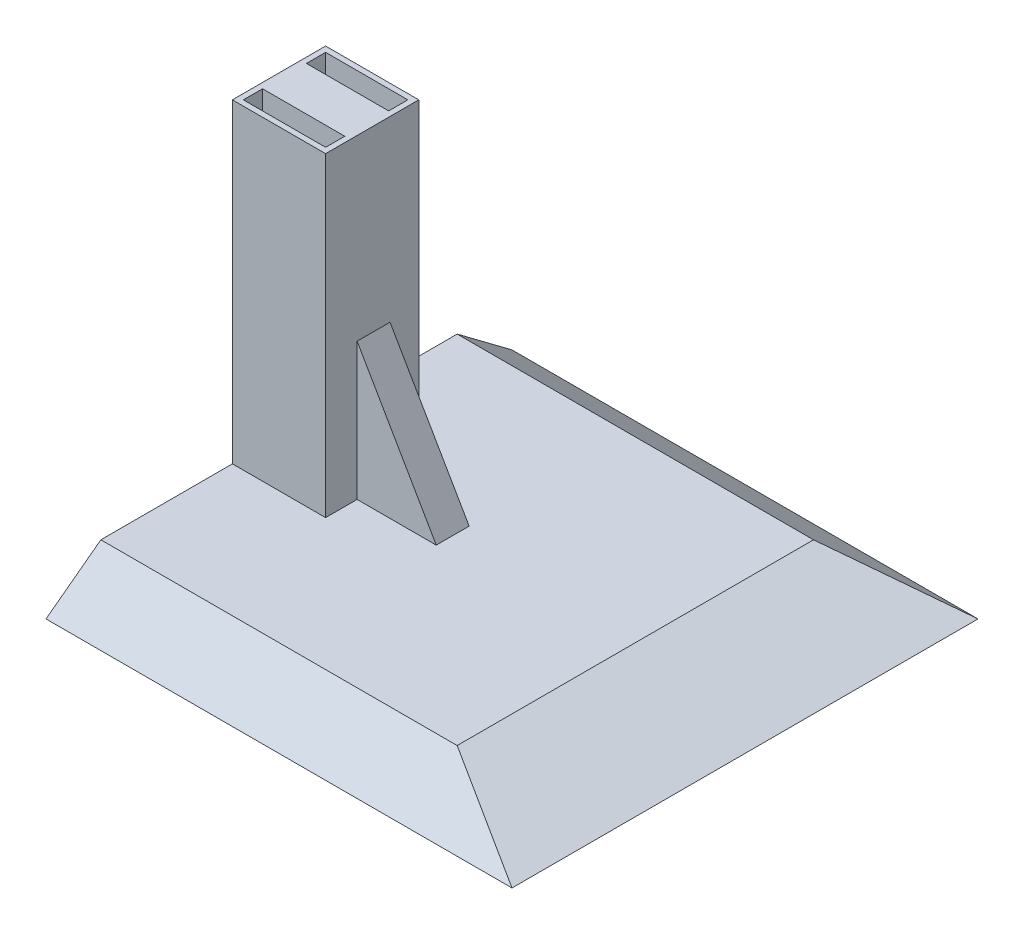
SolidWorks part; units mm, degrees
ref_plane "Front Plane" through (0, 0, 0) normal (0, 0, 1) x (1, 0, 0)
ref_plane "Top Plane" through (0, 0, 0) normal (0, 1, 0) x (1, 0, 0)
ref_plane "Right Plane" through (0, 0, 0) normal (1, 0, 0) x (0, 0, -1)
sketch "Sketch2" plane through (0, 0, 0) normal (0, 1, 0) x (1, 0, 0)
  line L1 (-42.5, -42.5) -> (42.5, -42.5)
  line L2 (-42.5, -42.5) -> (-42.5, 42.5)
  line L3 (-42.5, 42.5) -> (42.5, 42.5)
  line L4 (42.5, -42.5) -> (42.5, 42.5)
  line L5 (-42.5, -42.5) -> (42.5, 42.5) construction
  line L6 (-42.5, 42.5) -> (42.5, -42.5) construction
  point P0 (0, 0)
  dimension "D1" = 85
  dimension "D2" = 85
ref_plane "Plane1" through (0, 7.5, 0) normal (0, 1, 0) x (1, 0, 0)
sketch "Sketch3" plane through (0, 7.5, 0) normal (0, 1, 0) x (1, 0, 0)
  line L1 (22.5, -32.5) -> (-42.5, -32.5)
  line L2 (22.5, -32.5) -> (22.5, 32.5)
  line L3 (22.5, 32.5) -> (-42.5, 32.5)
  line L4 (-42.5, -32.5) -> (-42.5, 32.5)
  line L5 (22.5, -32.5) -> (-42.5, 32.5) construction
  line L6 (22.5, 32.5) -> (-42.5, -32.5) construction
  line L11 (-42.5, -42.5) -> (-42.5, 42.5) construction
  line L12 (-42.5, 42.5) -> (42.5, 42.5) construction
  dimension "D1" = 65
  dimension "D2" = 10
loft "Loft1" add profiles "Sketch2", "Sketch3"
sketch "Sketch10" plane through (0, 7.5, 0) normal (0, 1, 0) x (1, 0, 0)
  line L0 (-42.5, 32.5) -> (-42.5, -32.5) construction
  line L1 (-25.5, -8.5) -> (-42.5, -8.5)
  line L2 (-25.5, -8.5) -> (-25.5, 8.5)
  line L3 (-25.5, 8.5) -> (-42.5, 8.5)
  line L4 (-42.5, -8.5) -> (-42.5, 8.5)
  line L5 (-25.5, -8.5) -> (-42.5, 8.5) construction
  line L6 (-25.5, 8.5) -> (-42.5, -8.5) construction
  line L7 (-42.5, -32.5) -> (22.5, -32.5) construction
  point P0 (-34, 0)
  dimension "D1" = 32.5
  dimension "D2" = 17
  dimension "D3" = 17
extrude "Boss-Extrude5" add sketch "Sketch10" along normal blind 57.5 contours L2 L1 L4 L3
sketch "Sketch11" plane through (0, 65, 0) normal (0, 1, 0) x (1, 0, 0)
  line L0 (-42.5, -8.5) -> (-42.5, 8.5) construction
  line L1 (-26.5, -7.5) -> (-41.5, -7.5)
  line L2 (-26.5, -7.5) -> (-26.5, 7.5)
  line L3 (-26.5, 7.5) -> (-41.5, 7.5)
  line L4 (-41.5, -7.5) -> (-41.5, 7.5)
  line L5 (-26.5, -7.5) -> (-41.5, 7.5) construction
  line L6 (-26.5, 7.5) -> (-41.5, -7.5) construction
  line L7 (-25.5, 8.5) -> (-42.5, 8.5) construction
  line L10 (-26.5, -4) -> (-41.5, -4)
  line L11 (-26.5, -4) -> (-26.5, 4)
  line L12 (-26.5, 4) -> (-41.5, 4)
  line L13 (-41.5, -4) -> (-41.5, 4)
  line L14 (-26.5, -4) -> (-41.5, 4) construction
  line L15 (-26.5, 4) -> (-41.5, -4) construction
  point P0 (-34, 0)
  point P8 (-34, 0)
  dimension "D1" = 8.5
  dimension "D2" = 8.5
  dimension "D3" = 15
  dimension "D4" = 15
  dimension "D5" = 8
extrude "Cut-Extrude1" cut sketch "Sketch11" against normal blind 25 contours L12 L2 L3 L4 | L2 L10 L4 L1
sketch "Sketch14" plane through (0, 0, 8.5) normal (0, 0, 1) x (1, 0, 0)
  line L0 (-25.5, 32.5) -> (-11.0662, 7.5)
  line L1 (-25.5, 65) -> (-25.5, 7.5) construction
  line L2 (-42.5, 7.5) -> (22.5, 7.5) construction
  line L3 (-25.5, 32.5) -> (-25.5, 7.5)
  line L4 (-25.5, 7.5) -> (-11.0662, 7.5)
  dimension "D1" = 60
  dimension "D2" = 25
extrude "Boss-Extrude6" add sketch "Sketch14" against normal blind 6 from offset 5.75
